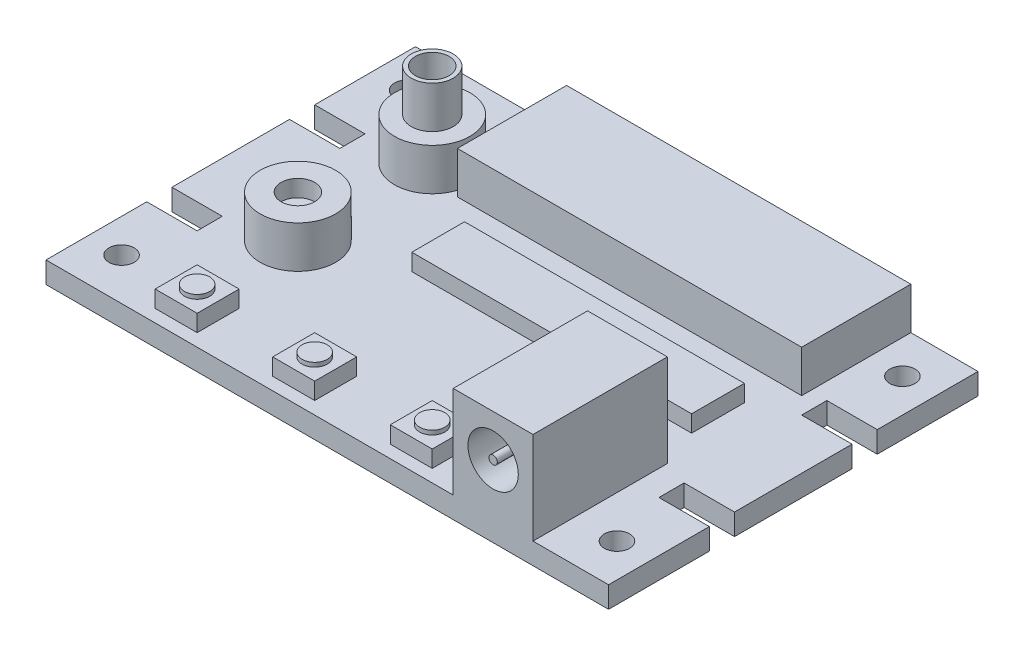
SolidWorks part; units mm, degrees
material "6061-T6 (SS)"
ref_plane "Front Plane" through (0, 0, 0) normal (0, 0, 1) x (1, 0, 0)
ref_plane "Top Plane" through (0, 0, 0) normal (0, 1, 0) x (1, 0, 0)
ref_plane "Right Plane" through (0, 0, 0) normal (1, 0, 0) x (0, 0, -1)
sketch "Sketch1" plane through (0, 0, 0) normal (0, 1, 0) x (1, 0, 0)
  line L0 (-33.5, 10) -> (-33.5, 22)
  line L1 (33.5, -22) -> (-33.5, -22)
  line L2 (33.5, -22) -> (33.5, -10)
  line L3 (33.5, 22) -> (-33.5, 22)
  line L4 (-33.5, -22) -> (-33.5, -10)
  line L5 (33.5, -22) -> (-33.5, 22) construction
  line L6 (33.5, 22) -> (-33.5, -22) construction
  line L7 (-33.5, 10) -> (-27.5, 10)
  line L9 (-33.5, 7) -> (-27.5, 7)
  line L10 (-27.5, 10) -> (-27.5, 7)
  line L11 (-33.5, -7) -> (-27.5, -7)
  line L13 (-33.5, -10) -> (-27.5, -10)
  line L14 (-27.5, -7) -> (-27.5, -10)
  line L15 (33.5, -7) -> (27.5, -7)
  line L17 (33.5, -10) -> (27.5, -10)
  line L18 (27.5, -7) -> (27.5, -10)
  line L19 (33.5, 10) -> (27.5, 10)
  line L21 (33.5, 7) -> (27.5, 7)
  line L22 (27.5, 10) -> (27.5, 7)
  line L23 (-33.5, -7) -> (-33.5, 7)
  line L24 (33.5, -7) -> (33.5, 7)
  line L25 (33.5, 10) -> (33.5, 22)
  line L26 (-27.5, 7) -> (-27.5, -7) construction
  line L27 (-27.5, 0) -> (0, 0) construction
  point P0 (0, 0)
  dimension "D1" = 67
  dimension "D2" = 44
  dimension "D3" = 6
  dimension "D4" = 3
  dimension "D5" = 12
extrude "Boss-Extrude1" add sketch "Sketch1" along normal blind 2.54
sketch "Sketch2" plane through (0, 2.54, 0) normal (0, 1, 0) x (1, 0, 0)
  line L0 (-29.5, 17) -> (-29.5, 22) construction
  line L1 (-29.5, 17) -> (29.5, 17) construction
  line L2 (-29.5, 17) -> (-29.5, -17) construction
  line L3 (-29.5, -17) -> (29.5, -17) construction
  line L4 (29.5, 17) -> (29.5, -17) construction
  line L5 (33.5, 22) -> (-33.5, 22) construction
  line L6 (-29.5, 17) -> (-33.5, 17) construction
  line L7 (-33.5, 22) -> (-33.5, 10) construction
  line L8 (29.5, -17) -> (29.5, -22) construction
  line L9 (-33.5, -22) -> (33.5, -22) construction
  line L10 (29.5, -17) -> (33.5, -17) construction
  line L11 (33.5, -22) -> (33.5, -10) construction
  circle A0 centre (-29.5, -17) radius 1.5
  circle A1 centre (-29.5, 17) radius 1.5
  circle A2 centre (29.5, 17) radius 1.5
  circle A4 centre (29.5, -17) radius 1.5
  dimension "D3" = 3
  dimension "D1" = 4
  dimension "D2" = 5
extrude "Cut-Extrude1" cut sketch "Sketch2" against normal through all
sketch "Sketch3" plane through (0, 2.54, 0) normal (0, 1, 0) x (1, 0, 0)
  line L0 (-33.5, 22) -> (-33.5, 10) construction
  line L1 (33.5, 22) -> (-33.5, 22) construction
  line L2 (-33.5, 7) -> (-33.5, -7) construction
  line L3 (-33.5, -22) -> (33.5, -22) construction
  circle A0 centre (-20.5, 11) radius 4.5
  circle A1 centre (-20.5, -5) radius 4.5
  dimension "D3" = 9
  dimension "D4" = 9
  dimension "D1" = 13
  dimension "D2" = 11
  dimension "D5" = 13
  dimension "D6" = 17
extrude "Boss-Extrude2" add sketch "Sketch3" along normal blind 5
sketch "Sketch4" plane through (0, 7.54, 0) normal (0, 1, 0) x (1, 0, 0)
  circle A0 centre (-20.5, 11) radius 2.5
  circle A1 centre (-20.5, 11) radius 2
  dimension "D1" = 5
  dimension "D2" = 4
extrude "Boss-Extrude3" add sketch "Sketch4" along normal blind 5
sketch "Sketch5" plane through (0, 7.54, 0) normal (0, 1, 0) x (1, 0, 0)
  circle A0 centre (-20.5, -5) radius 2
  dimension "D1" = 4
extrude "Cut-Extrude2" cut sketch "Sketch5" against normal blind 2
sketch "Sketch6" plane through (0, 2.54, 0) normal (0, 1, 0) x (1, 0, 0)
  line L5 (33.5, 22) -> (-33.5, 22) construction
  line L6 (-15.5, 22) -> (25.5, 22)
  line L7 (-15.5, 22) -> (-15.5, 9)
  line L8 (-15.5, 9) -> (25.5, 9)
  line L9 (25.5, 22) -> (25.5, 9)
  line L10 (33.5, 10) -> (33.5, 22) construction
  dimension "D1" = 13
  dimension "D2" = 41
  dimension "D3" = 8
extrude "Boss-Extrude4" add sketch "Sketch6" along normal blind 5
sketch "Sketch7" plane through (0, 2.54, 0) normal (0, 1, 0) x (1, 0, 0)
  line L0 (-33.5, -22) -> (33.5, -22) construction
  line L9 (-22, -20.5) -> (-17, -20.5)
  line L10 (-22, -20.5) -> (-22, -15.5)
  line L11 (-22, -15.5) -> (-17, -15.5)
  line L12 (-17, -20.5) -> (-17, -15.5)
  line L13 (-22, -20.5) -> (-17, -15.5) construction
  line L14 (-22, -15.5) -> (-17, -20.5) construction
  line L15 (-8, -20.5) -> (-3, -20.5)
  line L16 (-8, -20.5) -> (-8, -15.5)
  line L17 (-8, -15.5) -> (-3, -15.5)
  line L18 (-3, -20.5) -> (-3, -15.5)
  line L19 (-8, -20.5) -> (-3, -15.5) construction
  line L20 (-8, -15.5) -> (-3, -20.5) construction
  line L21 (6, -20.5) -> (11, -20.5)
  line L22 (6, -20.5) -> (6, -15.5)
  line L23 (6, -15.5) -> (11, -15.5)
  line L24 (11, -20.5) -> (11, -15.5)
  line L25 (6, -20.5) -> (11, -15.5) construction
  line L26 (6, -15.5) -> (11, -20.5) construction
  line L27 (-25.5, -22) -> (14.5, -22) construction
  line L28 (-25.5, -22) -> (-25.5, -14) construction
  line L29 (-25.5, -14) -> (14.5, -14) construction
  line L30 (14.5, -22) -> (14.5, -14) construction
  line L31 (-33.5, -10) -> (-33.5, -22) construction
  line L32 (-19.5, -18) -> (-5.5, -18) construction
  line L33 (-5.5, -18) -> (8.5, -18) construction
  line L34 (-19.5, -18) -> (-25.5, -18) construction
  line L35 (8.5, -18) -> (14.5, -18) construction
  point P0 (-19.5, -18)
  point P5 (-5.5, -18)
  point P10 (8.5, -18)
  point P28 (7.5549, -18)
  dimension "D1" = 8
  dimension "D2" = 40
  dimension "D3" = 8
  dimension "D4" = 5
  dimension "D5" = 6
extrude "Boss-Extrude5" add sketch "Sketch7" along normal blind 2
sketch "Sketch8" plane through (0, 4.54, 0) normal (0, 1, 0) x (1, 0, 0)
  line L0 (-22, -20.5) -> (-17, -15.5) construction
  line L1 (-8, -20.5) -> (-3, -15.5) construction
  line L2 (6, -20.5) -> (11, -15.5) construction
  circle A0 centre (-19.5, -18) radius 1.5
  circle A1 centre (-5.5, -18) radius 1.5
  circle A2 centre (8.5, -18) radius 1.5
  dimension "D1" = 3
extrude "Boss-Extrude6" add sketch "Sketch8" along normal blind 0.5
sketch "Sketch9" plane through (0, 2.54, 0) normal (0, 1, 0) x (1, 0, 0)
  line L0 (-33.5, -22) -> (33.5, -22) construction
  line L1 (15, -22) -> (24.5, -22)
  line L2 (15, -22) -> (15, -6)
  line L3 (15, -6) -> (24.5, -6)
  line L4 (24.5, -22) -> (24.5, -6)
  line L5 (33.5, -22) -> (33.5, -10) construction
  dimension "D1" = 9.5
  dimension "D2" = 16
  dimension "D3" = 9
extrude "Boss-Extrude7" add sketch "Sketch9" along normal blind 11
sketch "Sketch10" plane through (0, 0, 22) normal (0, 0, 1) x (1, 0, 0)
  line L0 (19.75, 8.54) -> (19.75, 13.54) construction
  line L1 (15, 13.54) -> (24.5, 13.54) construction
  circle A0 centre (19.75, 8.54) radius 3
  circle A1 centre (19.75, 8.54) radius 0.5
  dimension "D1" = 1
  dimension "D2" = 6
  dimension "D3" = 5
extrude "Cut-Extrude3" cut sketch "Sketch10" against normal blind 10
sketch "Sketch11" plane through (0, 2.54, 0) normal (0, 1, 0) x (1, 0, 0)
  line L1 (-10.5143, 4.8604) -> (22.8141, 4.8604)
  line L2 (-10.5143, 4.8604) -> (-10.5143, -1.4218)
  line L3 (-10.5143, -1.4218) -> (22.8141, -1.4218)
  line L4 (22.8141, 4.8604) -> (22.8141, -1.4218)
extrude "Boss-Extrude8" add sketch "Sketch11" along normal blind 2
sketch "Sketch12" plane through (0, 0, 0) normal (0, -1, 0) x (1, 0, 0)
  line L0 (33.5, 7) -> (33.5, -7) construction
  line L1 (9.5, 4) -> (17.5, 4)
  line L2 (9.5, 4) -> (9.5, -2)
  line L3 (9.5, -2) -> (17.5, -2)
  line L4 (17.5, 4) -> (17.5, -2)
  line L5 (33.5, -22) -> (-33.5, -22) construction
  dimension "D1" = 16
  dimension "D2" = 20
  dimension "D3" = 8
  dimension "D4" = 6
extrude "Boss-Extrude9" add sketch "Sketch12" along normal blind 2
sketch "Sketch13" plane through (0, -2, 0) normal (0, -1, 0) x (1, 0, 0)
  line L0 (9.5, -2) -> (17.5, 4) construction
  line L1 (10.5, 3) -> (13.5, 3) construction
  line L2 (10.5, 3) -> (10.5, -1) construction
  line L3 (10.5, -1) -> (13.5, -1) construction
  line L5 (13.5, 3) -> (16.5, 3) construction
  line L6 (13.5, 3) -> (13.5, -1) construction
  line L7 (13.5, -1) -> (16.5, -1) construction
  line L8 (16.5, 3) -> (16.5, -1) construction
  line L9 (9.5, -2) -> (17.5, -2) construction
  circle A1 centre (10.5, 3) radius 0.5
  circle A2 centre (13.5, 3) radius 0.5
  circle A3 centre (16.5, 3) radius 0.5
  circle A4 centre (16.5, -1) radius 0.5
  circle A5 centre (13.5, -1) radius 0.5
  circle A6 centre (10.5, -1) radius 0.5
  point P11 (13.5, 1)
  dimension "D3" = 1
  dimension "D1" = 4
  dimension "D2" = 3
extrude "Boss-Extrude10" add sketch "Sketch13" along normal blind 4
